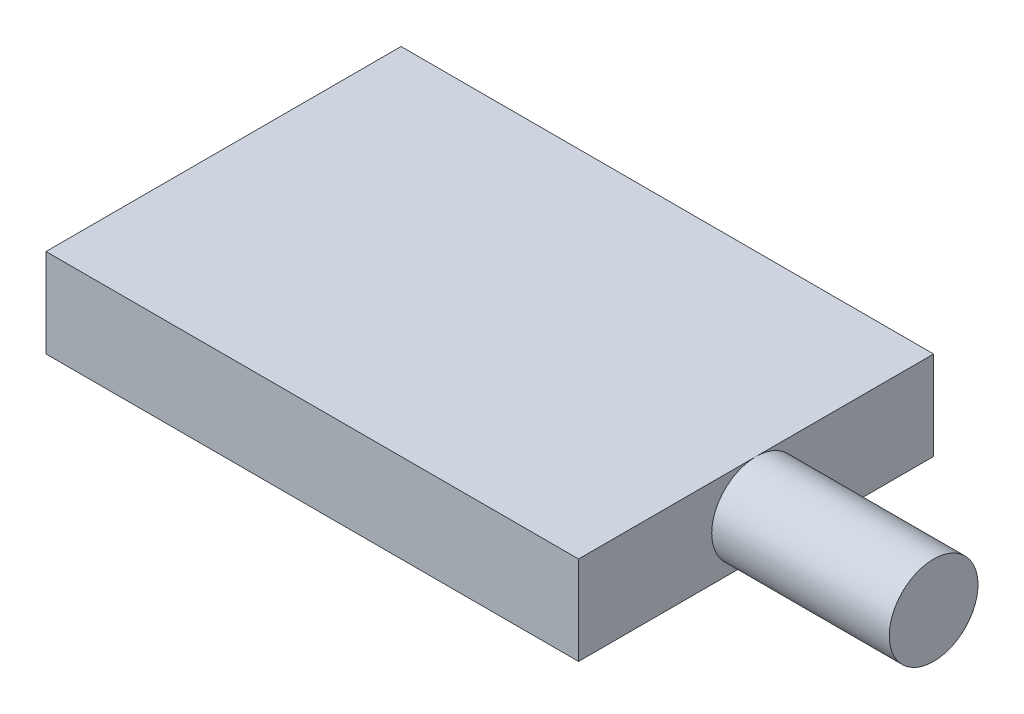
SolidWorks part; units mm, degrees
ref_plane "Front Plane" through (0, 0, 0) normal (0, 0, 1) x (1, 0, 0)
ref_plane "Top Plane" through (0, 0, 0) normal (0, 1, 0) x (1, 0, 0)
ref_plane "Right Plane" through (0, 0, 0) normal (1, 0, 0) x (0, 0, -1)
sketch "Sketch1" plane through (0, 0, 0) normal (0, 1, 0) x (1, 0, 0)
  line L1 (0, 0) -> (30, 0)
  line L2 (0, 0) -> (0, 20)
  line L3 (0, 20) -> (30, 20)
  line L4 (30, 0) -> (30, 20)
  dimension "D1" = 20
  dimension "D2" = 30
extrude "Boss-Extrude1" add sketch "Sketch1" along normal blind 5
sketch "Sketch2" plane through (30, 0, 0) normal (1, 0, 0) x (0, 0, -1)
  line L0 (10, 5) -> (10, 0) construction
  line L1 (0, 5) -> (20, 5) construction
  line L2 (0, 0) -> (20, 0) construction
  circle A0 centre (10, 2.5) radius 2.5
extrude "Boss-Extrude2" add sketch "Sketch2" along normal blind 10
